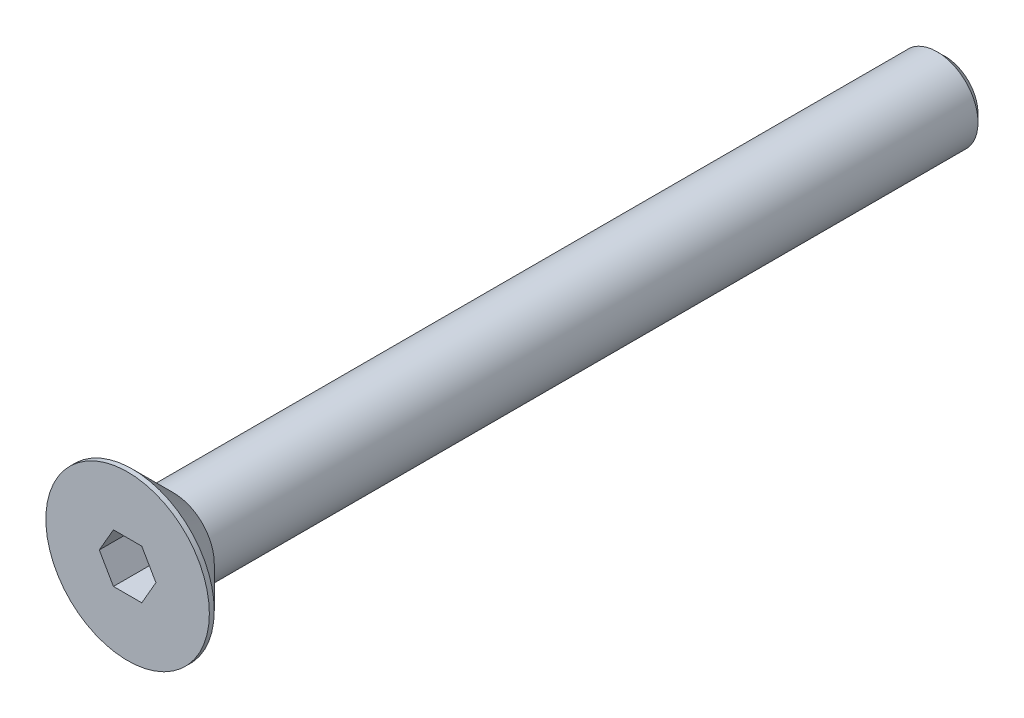
SolidWorks part; units mm, degrees
material "AISI 316 Stainless Steel Sheet (SS)"
ref_plane "Front Plane" through (0, 0, 0) normal (0, 0, 1) x (1, 0, 0)
ref_plane "Top Plane" through (0, 0, 0) normal (0, 1, 0) x (1, 0, 0)
ref_plane "Right Plane" through (0, 0, 0) normal (1, 0, 0) x (0, 0, -1)
sketch "Sketch1" plane through (0, 0, 0) normal (0, 1, 0) x (1, 0, 0)
  line L0 (2.5, 50) -> (0, 50)
  line L1 (0, 50) -> (0, 0)
  line L2 (0, 0) -> (5, 0)
  line L3 (5, 0) -> (5, 0.3)
  line L4 (5, 0.3) -> (2.5, 2.8)
  line L5 (2.5, 2.8) -> (2.5, 50)
  line L6 (0, 50) -> (0, 0) construction
  dimension "D1" = 50
  dimension "D2" = 5
  dimension "D3" = 2.5
  dimension "D4" = 2.5
  dimension "D6" = 0.3
revolve "Revolve1" add sketch "Sketch1" angle 360 about L6
sketch "Sketch2" plane through (0, 0, 0) normal (0, 0, 1) x (1, 0, 0)
  line L0 (-0.866, -1.5) -> (0.866, -1.5)
  line L1 (0.866, -1.5) -> (1.7321, 0)
  line L2 (1.7321, 0) -> (0.866, 1.5)
  line L3 (0.866, 1.5) -> (-0.866, 1.5)
  line L4 (-0.866, 1.5) -> (-1.7321, 0)
  line L5 (-1.7321, 0) -> (-0.866, -1.5)
extrude "Cut-Extrude1" cut sketch "Sketch2" against normal blind 3.3
chamfer "Chamfer1" distance 0.4908 angle 45 1 edges at (2.5, 0, -50)
